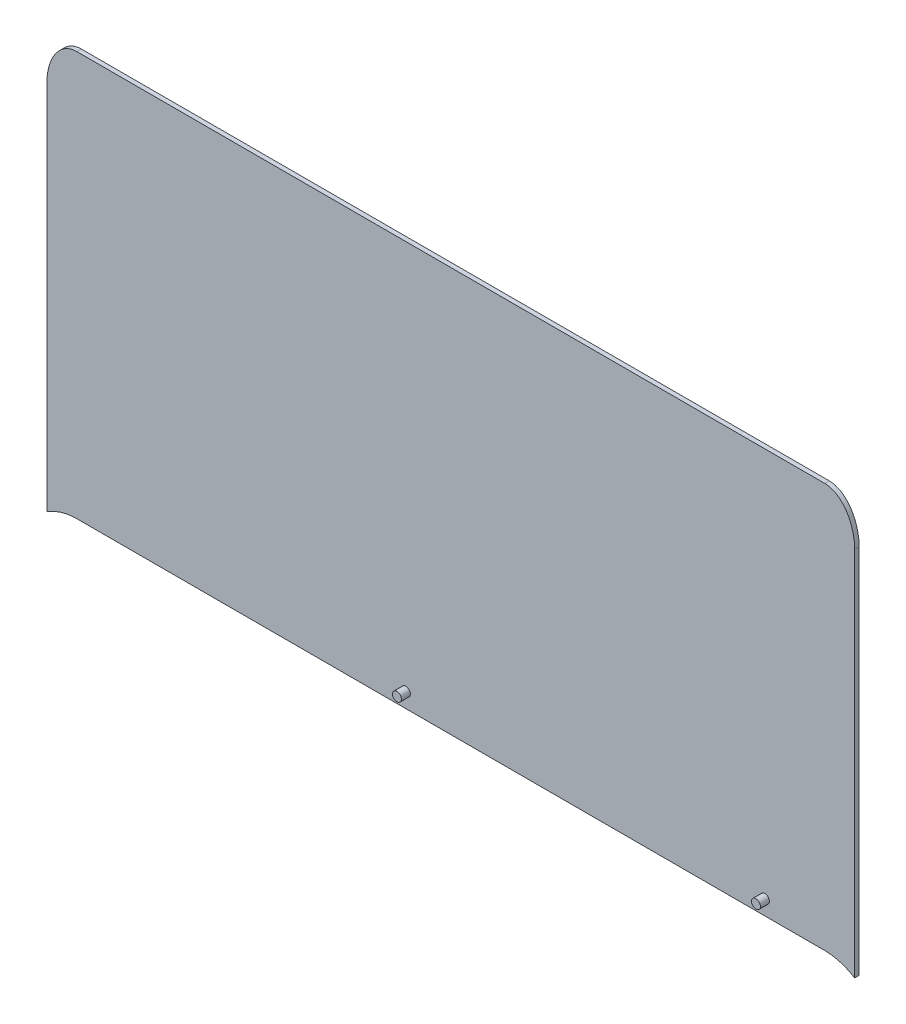
SolidWorks part; units mm, degrees
material "A-Glass Fiber"
ref_plane "Front Plane" through (0, 0, 0) normal (0, 0, 1) x (1, 0, 0)
ref_plane "Top Plane" through (0, 0, 0) normal (0, 1, 0) x (1, 0, 0)
ref_plane "Right Plane" through (0, 0, 0) normal (1, 0, 0) x (0, 0, -1)
sketch "Sketch1" plane through (0, 0, 0) normal (0, 0, 1) x (1, 0, 0)
  line L4 (250, 382.2089) -> (-250, 382.2089)
  line L5 (270, 376.3056) -> (270, 624.3409)
  line L6 (250, 652.6252) -> (-250, 652.6252)
  line L7 (-270, 624.3409) -> (-270, 376.3056)
  ellipse E4 centre (-250, 311.4982) end of major axis (-250, 382.2089) minor radius 50 (-250, 382.2089) -> (-270, 376.3056) ccw
  ellipse E5 centre (250, 311.4982) end of major axis (250, 240.7876) minor radius 50 (270, 376.3056) -> (250, 382.2089) ccw
  ellipse E6 centre (250, 624.3409) end of major axis (250, 596.0567) minor radius 20 (270, 624.3409) -> (250, 652.6252) ccw
  ellipse E7 centre (-250, 624.3409) end of major axis (-250, 652.6252) minor radius 20 (-250, 652.6252) -> (-270, 624.3409) ccw
extrude "Boss-Extrude1" add sketch "Sketch1" against normal blind 3
sketch "Sketch2" plane through (0, 0, 0) normal (0, 0, 1) x (1, 0, 0)
  line L0 (-250, 382.2089) -> (250, 382.2089) construction
  circle A0 centre (-30, 392.2089) radius 3
  circle A1 centre (210, 392.2089) radius 3
  point P4 (0, 382.2089)
  dimension "D1" = 6
  dimension "D4" = 6
  dimension "D2" = 30
  dimension "D3" = 10
  dimension "D5" = 240
  dimension "D6" = 10
extrude "Boss-Extrude2" add sketch "Sketch2" along normal blind 6
